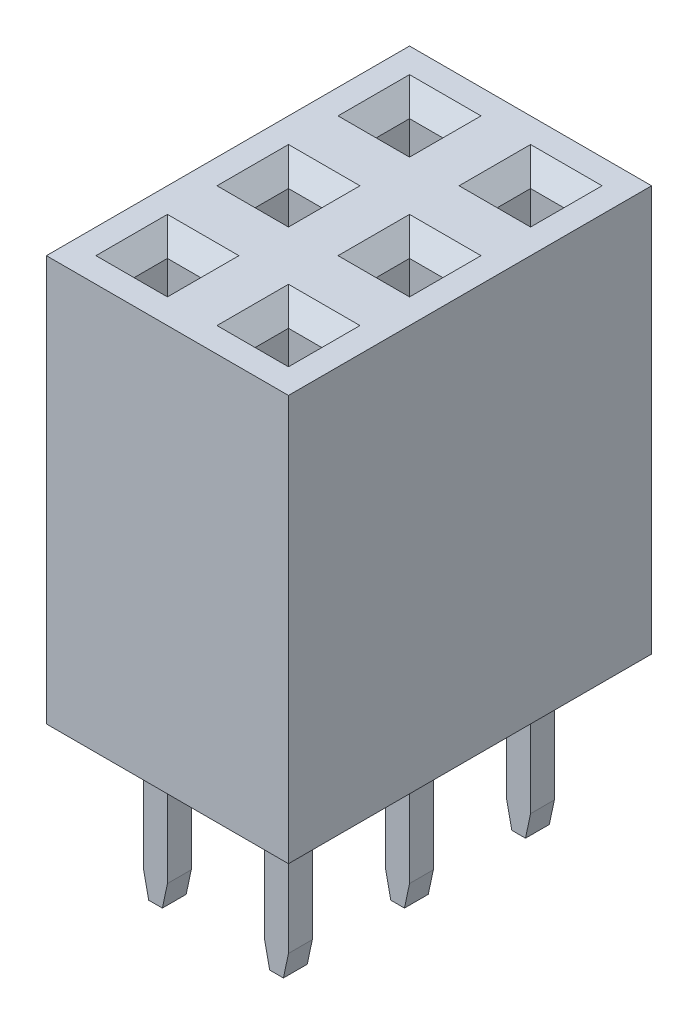
SolidWorks part; units mm, degrees
ref_plane "Спереди" through (0, 0, 0) normal (0, 0, 1) x (1, 0, 0)
ref_plane "Сверху" through (0, 0, 0) normal (0, 1, 0) x (1, 0, 0)
ref_plane "Справа" through (0, 0, 0) normal (1, 0, 0) x (0, 0, -1)
ref_plane "Плоскость1" through (0, 0, 0) normal (0, 1, 0) x (-1, 0, 0)
sketch "Эскиз1" plane through (0, 0, 0) normal (0, 1, 0) x (-1, 0, 0)
  line L0 (0, 0) -> (-5.5295, 0) construction
  line L1 (0, 0) -> (0, -2.1715) construction
  line L2 (-1.27, 1.27) -> (1.27, 1.27)
  line L3 (-1.27, 1.27) -> (-1.27, -1.27)
  line L4 (-1.27, -1.27) -> (1.27, -1.27)
  line L5 (1.27, 1.27) -> (1.27, -1.27)
  point P0 (-1.27, 1.27)
  point P1 (1.27, -1.27)
  point P2 (-1.27, -1.27)
  point P3 (1.27, 1.27)
  dimension "D1" = 2.54
  dimension "D6" = 1.27
extrude "Бобышка-Вытянуть1" add sketch "Эскиз1" along normal blind 8.51
sketch "Эскиз4" plane through (0, 8.51, 0) normal (0, 1, 0) x (1, 0, 0)
  line L0 (0, 0) -> (0.806, 0) construction
  line L1 (0, 0) -> (0, 1.2961) construction
  line L3 (-0.35, 0.35) -> (0.35, 0.35)
  line L4 (-0.35, 0.35) -> (-0.35, -0.35)
  line L5 (-0.35, -0.35) -> (0.35, -0.35)
  line L6 (0.35, 0.35) -> (0.35, -0.35)
  dimension "D1" = 0.7
extrude "Вырез-Вытянуть1" cut sketch "Эскиз4" against normal blind 8.21
chamfer "Фаска3" distance 0.4 angle 45 4 edges at (0.35, 8.51, 0) (0, 8.51, -0.35) (0, 8.51, 0.35) (-0.35, 8.51, 0)
sketch "Эскиз2" plane through (0, 0, 0) normal (0, 1, 0) x (-1, 0, 0)
  line L0 (0, 0) -> (0, -0.4454) construction
  line L1 (0.25, 0.25) -> (-0.25, 0.25)
  line L2 (0.25, 0.25) -> (0.25, -0.25)
  line L3 (0.25, -0.25) -> (-0.25, -0.25)
  line L4 (-0.25, 0.25) -> (-0.25, -0.25)
  line L5 (0, 0) -> (-0.4704, 0) construction
  dimension "D1" = 0.5
  dimension "D2" = 0.5
extrude "Бобышка-Вытянуть2" add sketch "Эскиз2" against normal blind 3.15
chamfer "Фаска2" distance 0.5 angle 12 2 edges at (0.25, -3.15, 0) (-0.25, -3.15, 0)
pattern_linear "Линейный массив1" count 3 spacing 2.54 along (0, 0, -1) count 2 spacing 2.54 along (-1, 0, 0) of "Бобышка-Вытянуть1", "Вырез-Вытянуть1", "Фаска3", "Бобышка-Вытянуть2", "Фаска2"
equation "\"D6@Эскиз1\"=2.54/2"
